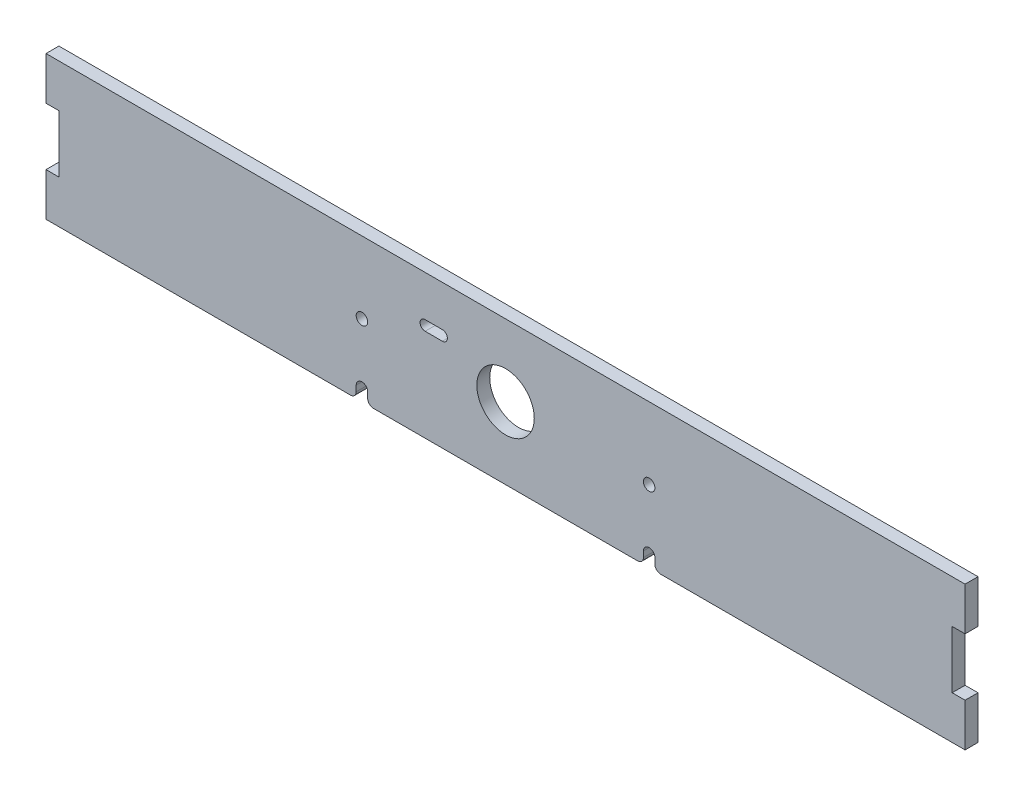
SolidWorks part; units mm, degrees
ref_plane "Front Plane" through (0, 0, 0) normal (0, 0, 1) x (1, 0, 0)
ref_plane "Top Plane" through (0, 0, 0) normal (0, 1, 0) x (1, 0, 0)
ref_plane "Right Plane" through (0, 0, 0) normal (1, 0, 0) x (0, 0, -1)
sketch "Sketch1" plane through (0, 0, 0) normal (0, 0, 1) x (1, 0, 0)
  line L1 (-203.2, -31.75) -> (203.2, -31.75)
  line L2 (-203.2, -31.75) -> (-203.2, 31.75)
  line L3 (-203.2, 31.75) -> (203.2, 31.75)
  line L4 (203.2, -31.75) -> (203.2, 31.75)
  line L5 (-203.2, -31.75) -> (203.2, 31.75) construction
  line L6 (-203.2, 31.75) -> (203.2, -31.75) construction
  point P0 (0, 0)
  dimension "D1" = 406.4
  dimension "D2" = 63.5
extrude "Boss-Extrude1" add sketch "Sketch1" along normal blind 5.715
sketch "Sketch2" plane through (0, 0, 0) normal (0, 0, 1) x (1, 0, 0)
  circle A0 centre (0, 0) radius 12.7
  dimension "D1" = 25.4
extrude "Seed Hole" cut sketch "Sketch2" along normal through all both and the other way through all
sketch "Sketch3" plane through (0, 0, 0) normal (0, 0, 1) x (1, 0, 0)
  line L0 (-63.5, 0) -> (63.5, 0) construction
  circle A0 centre (-63.5, 0) radius 2.54
  circle A1 centre (63.5, 0) radius 2.54
  point P3 (0, 0)
  dimension "D2" = 5.08
  dimension "D1" = 127
extrude "LED Mount" cut sketch "Sketch3" along normal through all
sketch "Sketch4" plane through (0, 0, 5.715) normal (0, 0, 1) x (1, 0, 0)
  line L0 (-63.5, -26.67) -> (-63.5, -36.83) construction
  line L1 (-60.96, -26.67) -> (-60.96, -36.83)
  line L2 (-66.04, -26.67) -> (-66.04, -36.83)
  line L3 (63.5, -26.67) -> (63.5, -36.83) construction
  line L4 (66.04, -26.67) -> (66.04, -36.83)
  line L5 (60.96, -26.67) -> (60.96, -36.83)
  line L7 (-63.5, 0) -> (-63.5, -31.75) construction
  line L8 (-203.2, -31.75) -> (203.2, -31.75) construction
  line L9 (63.5, 0) -> (63.5, -31.75) construction
  arc A0 (-60.96, -26.67) -> (-66.04, -26.67) centre (-63.5, -26.67) ccw
  arc A1 (-66.04, -36.83) -> (-60.96, -36.83) centre (-63.5, -36.83) ccw
  arc A2 (66.04, -26.67) -> (60.96, -26.67) centre (63.5, -26.67) ccw
  arc A3 (60.96, -36.83) -> (66.04, -36.83) centre (63.5, -36.83) ccw
  point P2 (-63.5, -31.75)
  point P7 (63.5, -31.75)
  dimension "D2" = 2.54
  dimension "D1" = 5.08
extrude "IR Sensor Wire Keeper" cut sketch "Sketch4" against normal through all both and the other way through all
fillet "Fillet1" radius 2.54 4 edges at (60.96, -31.75, 2.8575) (66.04, -31.75, 2.8575) (-66.04, -31.75, 2.8575) (-60.96, -31.75, 2.8575)
sketch "Sketch5" plane through (0, 0, 5.715) normal (0, 0, 1) x (1, 0, 0)
  line L0 (-35.56, 11.43) -> (-27.94, 11.43) construction
  line L1 (-35.56, 13.6525) -> (-27.94, 13.6525)
  line L2 (-35.56, 9.2075) -> (-27.94, 9.2075)
  arc A0 (-35.56, 13.6525) -> (-35.56, 9.2075) centre (-35.56, 11.43) ccw
  arc A1 (-27.94, 9.2075) -> (-27.94, 13.6525) centre (-27.94, 11.43) ccw
  point P2 (-31.75, 11.43)
  dimension "D1" = 4.445
  dimension "D2" = 11.43
  dimension "D3" = 7.62
  dimension "D4" = 31.75
extrude "Seed Switch Mount" cut sketch "Sketch5" against normal through all
sketch "Sketch6" plane through (0, 0, 5.715) normal (0, 0, 1) x (1, 0, 0)
  line L0 (-203.2, 31.75) -> (-203.2, -31.75) construction
  line L1 (-203.2, 12.7) -> (-197.485, 12.7)
  line L2 (-203.2, 12.7) -> (-203.2, -12.7)
  line L3 (-203.2, -12.7) -> (-197.485, -12.7)
  line L4 (-197.485, 12.7) -> (-197.485, -12.7)
  line L5 (-197.485, 12.7) -> (-197.485, 31.75) construction
  line L6 (203.2, 31.75) -> (-203.2, 31.75) construction
  line L7 (-197.485, -12.7) -> (-197.485, -31.75) construction
  line L8 (-203.2, -31.75) -> (-68.58, -31.75) construction
  dimension "D1" = 5.715
  dimension "D2" = 19.05
extrude "Cut-Extrude6" cut sketch "Sketch6" against normal through all
mirror "Mirror1" about plane through (0, 0, 0) normal (1, 0, 0) of "Cut-Extrude6"
